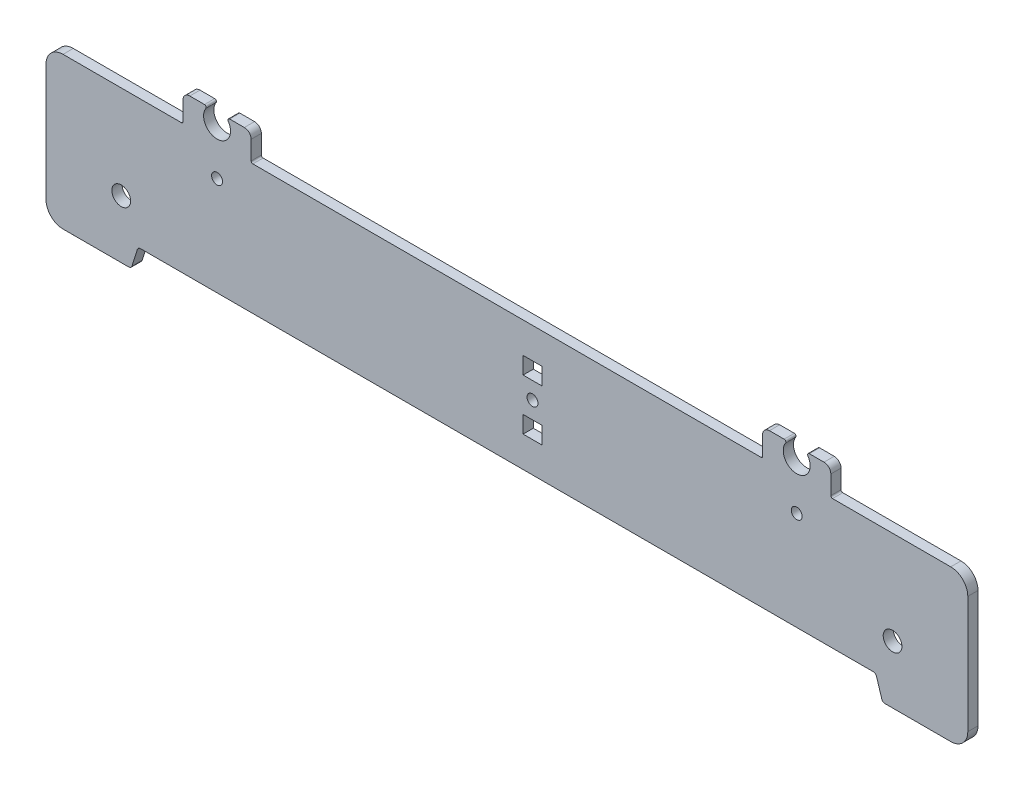
SolidWorks part; units mm, degrees
ref_plane "Alzado" through (0, 0, 0) normal (0, 0, 1) x (1, 0, 0)
ref_plane "Planta" through (0, 0, 0) normal (0, 1, 0) x (1, 0, 0)
ref_plane "Vista lateral" through (0, 0, 0) normal (1, 0, 0) x (0, 0, -1)
sketch "Model" plane through (0, 0, 0) normal (0, 0, 1) x (1, 0, 0)
  line L0 (146.3316, 52.0849) -> (71.6934, 52.0849)
  line L1 (71.1925, 52.5858) -> (71.1925, 58.0939)
  line L2 (69.1889, 60.0975) -> (64.8648, 60.0975)
  line L3 (57.4837, 60.0975) -> (53.1597, 60.0975)
  line L4 (51.1561, 58.0939) -> (51.1561, 52.5858)
  line L5 (50.6552, 52.0849) -> (20.9286, 52.0849)
  line L6 (20.9286, 52.0849) -> (15.9195, 52.0849)
  line L7 (10.9104, 47.0758) -> (10.9104, 12.6256)
  line L8 (15.9195, 7.6165) -> (35.2198, 7.6165)
  line L9 (36.1759, 8.3189) -> (37.7396, 13.3132)
  line L10 (38.6957, 14.0157) -> (146.3316, 14.0133)
  line L11 (146.3316, 52.0849) -> (220.9698, 52.0849)
  line L12 (221.4707, 52.5858) -> (221.4707, 58.0939)
  line L13 (223.4744, 60.0975) -> (227.7984, 60.0975)
  line L14 (235.1795, 60.0975) -> (239.5035, 60.0975)
  line L15 (241.5072, 58.0939) -> (241.5072, 52.5858)
  line L16 (242.0081, 52.0849) -> (271.7346, 52.0849)
  line L17 (271.7346, 52.0849) -> (276.7437, 52.0849)
  line L18 (281.7528, 47.0758) -> (281.7528, 12.6256)
  line L19 (276.7437, 7.6165) -> (257.4434, 7.6165)
  line L20 (256.4874, 8.3189) -> (254.9236, 13.3132)
  line L21 (253.9675, 14.0157) -> (146.3316, 14.0133)
  line L22 (151.0903, 43.0582) -> (151.0903, 38.0582)
  line L23 (151.0903, 38.0582) -> (156.5903, 38.0582)
  line L24 (151.0903, 43.0582) -> (156.5903, 43.0582)
  line L25 (156.5903, 43.0582) -> (156.5903, 38.0582)
  line L26 (151.0903, 23.0309) -> (151.0903, 28.04)
  line L27 (151.0903, 28.04) -> (156.5903, 28.04)
  line L28 (151.0903, 23.0309) -> (156.5903, 23.0309)
  line L29 (156.5903, 23.0309) -> (156.5903, 28.04)
  circle A0 centre (61.1743, 43.0702) radius 1.6029
  circle A1 centre (231.4889, 43.0702) radius 1.6029
  circle A2 centre (153.8453, 33.0491) radius 1.6029
  circle A3 centre (33.0115, 24.6474) radius 2.755
  circle A4 centre (259.6517, 24.6474) radius 2.755
  arc A5 (71.1925, 52.5858) -> (71.6934, 52.0849) centre (71.6934, 52.5858) ccw
  arc A6 (71.1925, 58.0939) -> (69.1889, 60.0975) centre (69.1889, 58.0939) ccw
  arc A7 (64.8648, 60.0975) -> (64.4502, 59.3156) centre (64.8648, 59.5966) ccw
  arc A8 (57.8984, 59.3156) -> (64.4502, 59.3156) centre (61.1743, 57.0957) ccw
  arc A9 (57.8984, 59.3156) -> (57.4837, 60.0975) centre (57.4837, 59.5966) ccw
  arc A10 (53.1597, 60.0975) -> (51.1561, 58.0939) centre (53.1597, 58.0939) ccw
  arc A11 (50.6552, 52.0849) -> (51.1561, 52.5858) centre (50.6552, 52.5858) ccw
  arc A12 (15.9195, 52.0849) -> (10.9104, 47.0758) centre (15.9195, 47.0758) ccw
  arc A13 (10.9104, 12.6256) -> (15.9195, 7.6165) centre (15.9195, 12.6256) ccw
  arc A14 (35.2198, 7.6165) -> (36.1759, 8.3189) centre (35.2198, 8.6183) ccw
  arc A15 (38.6957, 14.0157) -> (37.7396, 13.3132) centre (38.6957, 13.0139) ccw
  arc A16 (220.9698, 52.0849) -> (221.4707, 52.5858) centre (220.9698, 52.5858) ccw
  arc A17 (223.4744, 60.0975) -> (221.4707, 58.0939) centre (223.4744, 58.0939) ccw
  arc A18 (228.2131, 59.3156) -> (227.7984, 60.0975) centre (227.7984, 59.5966) ccw
  arc A19 (228.2131, 59.3156) -> (234.7648, 59.3156) centre (231.4889, 57.0957) ccw
  arc A20 (235.1795, 60.0975) -> (234.7648, 59.3156) centre (235.1795, 59.5966) ccw
  arc A21 (241.5072, 58.0939) -> (239.5035, 60.0975) centre (239.5035, 58.0939) ccw
  arc A22 (241.5072, 52.5858) -> (242.0081, 52.0849) centre (242.0081, 52.5858) ccw
  arc A23 (281.7528, 47.0758) -> (276.7437, 52.0849) centre (276.7437, 47.0758) ccw
  arc A24 (276.7437, 7.6165) -> (281.7528, 12.6256) centre (276.7437, 12.6256) ccw
  arc A25 (256.4874, 8.3189) -> (257.4434, 7.6165) centre (257.4434, 8.6183) ccw
  arc A26 (254.9236, 13.3132) -> (253.9675, 14.0157) centre (253.9675, 13.0139) ccw
  dimension "D1" = 5.5
  dimension "D2" = 5.5
  dimension "D3" = 5.5
  dimension "D4" = 5
  dimension "D5" = 5
  dimension "D6" = 5.5
extrude "Saliente-Extruir1" add sketch "Model" along normal blind 3 contours A26 L20 A25 L19 A24 L18 A23 L17 L16 A22 L15 A21 L14 A20 A19 A18 L13 A17 L12 A16 L11 L0 A5 L1 A6 L2 A7 A8 A9 L3 A10 L4 A11 L5 L6 A12 L7 A13 L8 A14 L9 A15 L10 L21 A4 A3 A2
